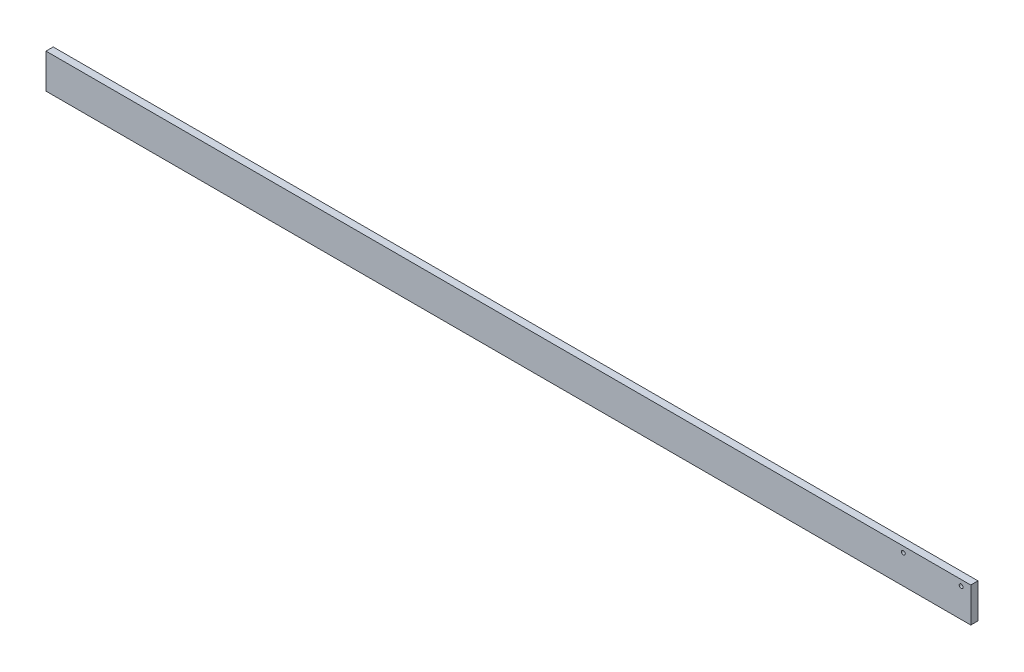
SolidWorks part; units mm, degrees
ref_plane "Front Plane" through (0, 0, 0) normal (0, 0, 1) x (1, 0, 0)
ref_plane "Top Plane" through (0, 0, 0) normal (0, 1, 0) x (1, 0, 0)
ref_plane "Right Plane" through (0, 0, 0) normal (1, 0, 0) x (0, 0, -1)
sketch "Sketch1" plane through (0, 0, 0) normal (0, 0, 1) x (1, 0, 0)
  line L1 (-304.8, -11.43) -> (304.8, -11.43)
  line L2 (-304.8, -11.43) -> (-304.8, 11.43)
  line L3 (-304.8, 11.43) -> (304.8, 11.43)
  line L4 (304.8, -11.43) -> (304.8, 11.43)
  line L5 (-304.8, -11.43) -> (304.8, 11.43) construction
  line L6 (-304.8, 11.43) -> (304.8, -11.43) construction
  point P0 (0, 0)
  dimension "D1" = 609.6
  dimension "D2" = 22.86
extrude "Boss-Extrude1" add sketch "Sketch1" along normal mid plane 4.7625
sketch "Sketch2" [suppressed] plane through (0, 0, 2.3813) normal (0, 0, 1) x (1, 0, 0)
  line L0 (304.8, -11.43) -> (304.8, 11.43) construction
  line L1 (304.8, 11.43) -> (228.6, 11.43)
  line L2 (304.8, 11.43) -> (304.8, -3.81)
  line L3 (304.8, -3.81) -> (228.6, -3.81)
  line L4 (228.6, 11.43) -> (228.6, -3.81)
  circle A0 centre (260.35, -7.62) radius 1.27
  circle A1 centre (298.45, -7.62) radius 1.27
  dimension "D6" = 2.54
  dimension "D7" = 2.54
  dimension "D1" = 15.24
  dimension "D2" = 76.2
  dimension "D3" = 44.45
  dimension "D4" = 6.35
  dimension "D5" = 3.81
extrude "Cut-Extrude1" [suppressed] cut sketch "Sketch2" against normal through all
sketch "Sketch3" [suppressed] plane through (0, 0, 2.3813) normal (0, 0, 1) x (1, 0, 0)
  line L0 (304.8, -11.43) -> (304.8, 11.43) construction
  line L1 (304.8, 11.43) -> (228.6, 11.43)
  line L2 (304.8, 11.43) -> (304.8, 3.81)
  line L3 (304.8, 3.81) -> (228.6, 3.81)
  line L4 (228.6, 11.43) -> (228.6, 3.81)
  circle A0 centre (260.35, 0) radius 1.27
  circle A1 centre (298.45, 0) radius 1.27
  dimension "D3" = 2.54
  dimension "D4" = 2.54
  dimension "D1" = 7.62
  dimension "D2" = 76.2
  dimension "D5" = 3.81
  dimension "D6" = 38.1
  dimension "D7" = 6.35
extrude "Cut-Extrude2" [suppressed] cut sketch "Sketch3" against normal through all
sketch "Sketch4" plane through (0, 0, 2.3813) normal (0, 0, 1) x (1, 0, 0)
  line L0 (304.8, 11.43) -> (-304.8, 11.43) construction
  line L1 (304.8, -11.43) -> (304.8, 11.43) construction
  circle A0 centre (260.35, 7.62) radius 1.27
  circle A1 centre (298.45, 7.62) radius 1.27
  dimension "D1" = 2.54
  dimension "D2" = 2.54
  dimension "D3" = 3.81
  dimension "D4" = 6.35
  dimension "D5" = 44.45
extrude "Cut-Extrude3" cut sketch "Sketch4" against normal through all
